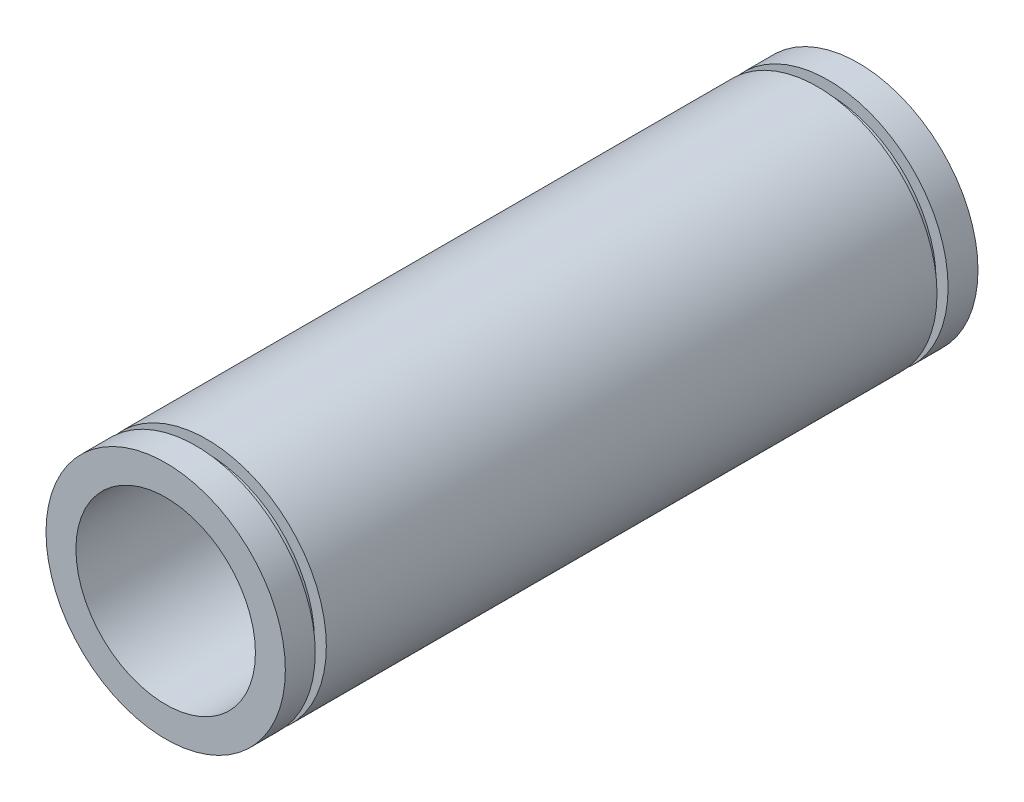
SolidWorks part; units mm, degrees
material "AISI 1020"
ref_plane "Front" through (0, 0, 0) normal (0, 0, 1) x (1, 0, 0)
ref_plane "Top" through (0, 0, 0) normal (0, 1, 0) x (1, 0, 0)
ref_plane "Right" through (0, 0, 0) normal (1, 0, 0) x (0, 0, -1)
sketch "Sketch1" plane through (0, 0, 0) normal (0, 0, 1) x (1, 0, 0)
  circle A0 centre (0, 0) radius 20
  dimension "D1" = 40
extrude "Boss-Extrude1" add sketch "Sketch1" along normal blind 52.8796
sketch "Sketch2" plane through (0, 0, 52.8796) normal (0, 0, 1) x (1, 0, 0)
  circle A0 centre (0, 0) radius 18
  circle A1 centre (0, 0) radius 20
  dimension "D1" = 36
  dimension "D2" = 40
extrude "Cut-Extrude2" cut sketch "Sketch2" against normal blind 1.85
sketch "Sketch6" plane through (0, 0, 52.8796) normal (0, 0, 1) x (1, 0, 0)
  circle A0 centre (0, 0) radius 20
  dimension "D1" = 40
extrude "Boss-Extrude2" add sketch "Sketch6" along normal blind 5
mirror "Mirror2" about plane through (0, 0, 0) normal (0, 0, 1) of bodies 106
sketch "Sketch7" plane through (0, 0, -57.8796) normal (0, 0, -1) x (-1, 0, 0)
  circle A0 centre (0, 0) radius 15
  dimension "D1" = 30
extrude "Cut-Extrude3" cut sketch "Sketch7" against normal through all both and the other way through all
